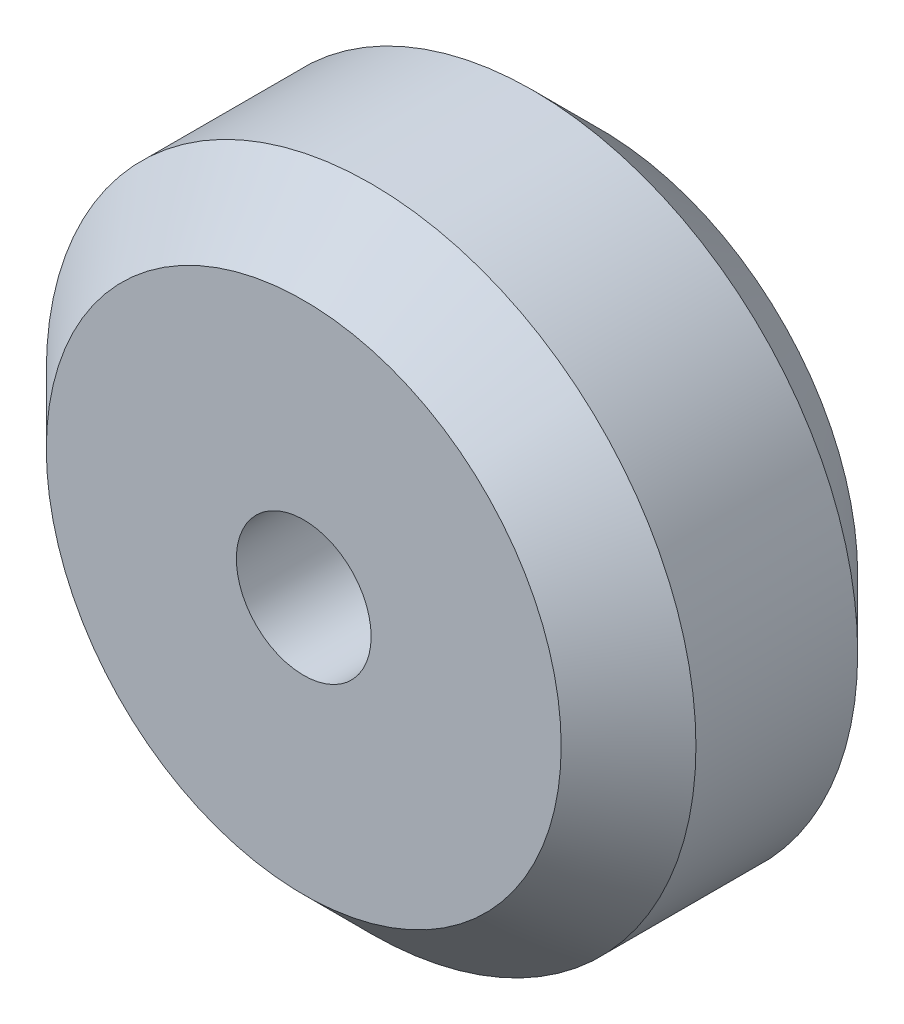
SolidWorks part; units mm, degrees
ref_plane "Front" through (0, 0, 0) normal (0, 0, 1) x (1, 0, 0)
ref_plane "Top" through (0, 0, 0) normal (0, 1, 0) x (1, 0, 0)
ref_plane "Right" through (0, 0, 0) normal (1, 0, 0) x (0, 0, -1)
sketch "Sketch1" plane through (0, 0, 0) normal (0, 0, 1) x (1, 0, 0)
  circle A0 centre (0, 0) radius 12.05
  circle A1 centre (0, 0) radius 2.5
extrude "Boss-Extrude1" add sketch "Sketch1" along normal blind 11
chamfer "Chamfer1" distance 2.5 angle 45 2 edges at (12.05, 0, 0) (12.05, 0, 11)
